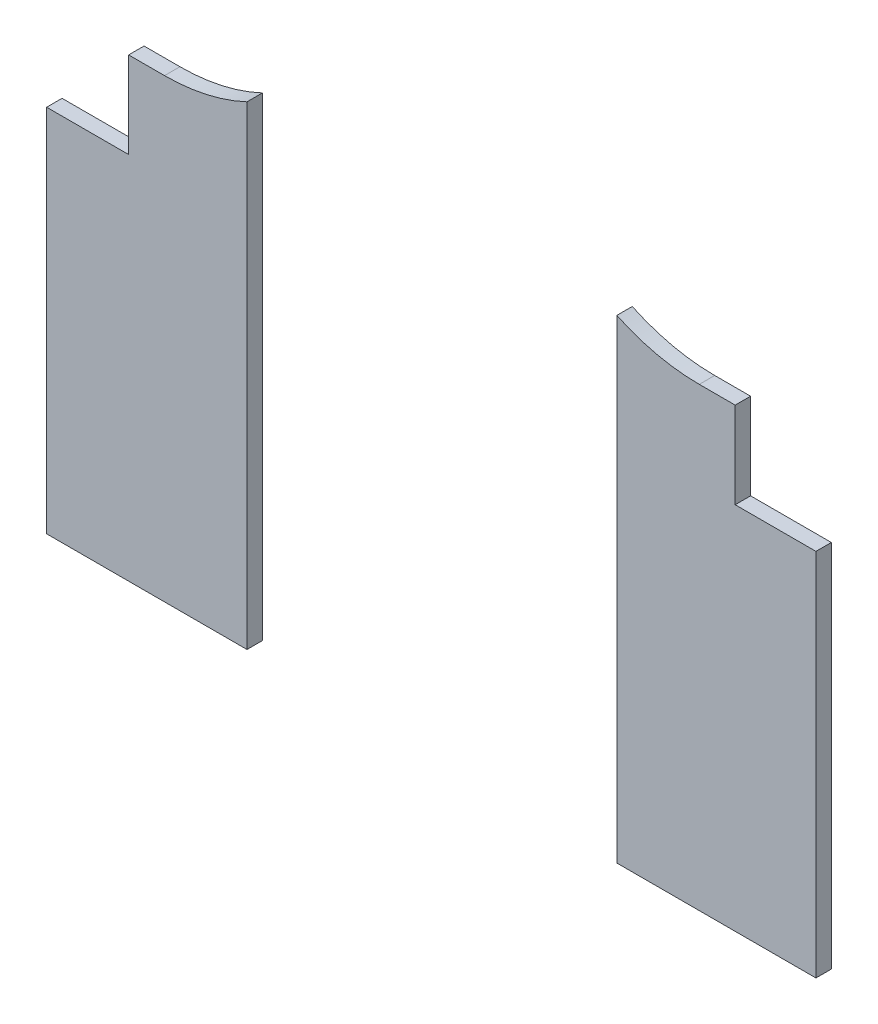
SolidWorks part; units mm, degrees
ref_plane "Front Plane" through (0, 0, 0) normal (0, 0, 1) x (1, 0, 0)
ref_plane "Top Plane" through (0, 0, 0) normal (0, 1, 0) x (1, 0, 0)
ref_plane "Right Plane" through (0, 0, 0) normal (1, 0, 0) x (0, 0, -1)
sketch "Sketch1" plane through (0, 0, 0) normal (0, 0, 1) x (1, 0, 0)
  line L0 (124.8, 0) -> (124.8, -267.4) construction
  line L1 (0, 0) -> (249.6, 0)
  line L2 (0, 0) -> (0, -267.4)
  line L3 (0, -267.4) -> (249.6, -267.4)
  line L4 (249.6, 0) -> (249.6, -267.4)
  line L7 (249.6, -267.4) -> (249.6, -100) construction
  line L8 (249.6, -267.4) -> (0, -267.4) construction
extrude "Boss-Extrude1" add sketch "Sketch1" along normal blind 5
sketch "Sketch5" plane through (0, 0, 5) normal (0, 0, 1) x (1, 0, 0)
  line L4 (0, -195.5612) -> (249.6, -195.5612)
  line L19 (151.0306, 0) -> (249.6, 0)
  line L26 (249.6, 0) -> (0, 0) construction
  line L29 (0, -195.5612) -> (0, -267.4)
  line L30 (0, -267.4) -> (249.6, -267.4)
  line L31 (249.6, -267.4) -> (249.6, -195.5612)
  line L34 (249.6, 0) -> (249.6, -75.6859)
  line L36 (249.6, -267.4) -> (249.6, 0) construction
  line L38 (223.3957, -75.6859) -> (250, -75.6859) construction
  line L39 (249.6, -75.6859) -> (223.3957, -75.6859)
  line L40 (223.3957, -75.6859) -> (223.3957, -47.6859)
  line L41 (223.3957, -47.6859) -> (211.7496, -47.6859)
  line L42 (98.9694, 0) -> (0, 0)
  line L43 (0, 0) -> (0, -75.6859)
  line L44 (0, 0) -> (0, -267.4) construction
  line L45 (0, -75.6859) -> (26.6043, -75.6859) construction
  line L46 (0, -75.6859) -> (26.6043, -75.6859)
  line L47 (26.6043, -75.6859) -> (26.6043, -47.6859)
  line L49 (26.6043, -75.6859) -> (26.6043, -47.6859) construction
  line L50 (26.6043, -47.6859) -> (38.2504, -47.6859)
  arc A5 (211.7496, -47.6859) -> (151.0306, 0) centre (211.7496, 14.8141) cw
  arc A8 (38.2504, -47.6859) -> (100.7504, 14.8141) centre (38.2504, 14.8141) ccw construction
  arc A11 (38.2504, -47.6859) -> (98.9694, 0) centre (38.2504, 14.8141) ccw
  arc A12 (153.4401, 37.3141) -> (211.7496, -47.6859) centre (211.7496, 14.8141) ccw construction
extrude "Cut-Extrude3" cut sketch "Sketch5" against normal through all
sketch "Sketch7" plane through (0, 0, 5) normal (0, 0, 1) x (1, 0, 0)
  line L0 (65, -195.5612) -> (185, -195.5612)
  line L1 (65, -195.5612) -> (65, 0)
  line L2 (185, -195.5612) -> (185, 0)
  line L3 (65, 0) -> (185, 0)
  line L4 (249.6, -195.5612) -> (0, -195.5612) construction
  line L6 (125, 0) -> (125, -195.5612) construction
  line L7 (151.0306, 0) -> (98.9694, 0) construction
  point P7 (125, 0)
  dimension "D1" = 120
extrude "Cut-Extrude4" cut sketch "Sketch7" against normal through all
